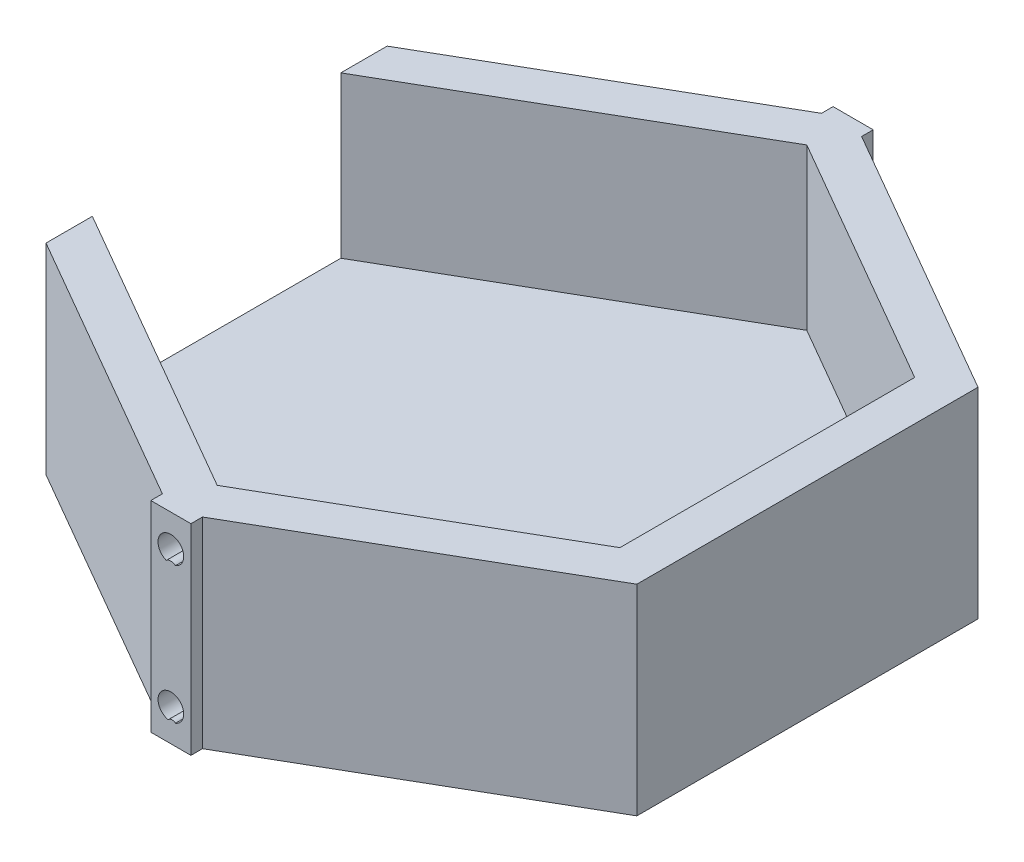
SolidWorks part; units mm, degrees
ref_plane "Front Plane" through (0, 0, 0) normal (0, 0, 1) x (1, 0, 0)
ref_plane "Top Plane" through (0, 0, 0) normal (0, 1, 0) x (1, 0, 0)
ref_plane "Right Plane" through (0, 0, 0) normal (1, 0, 0) x (0, 0, -1)
sketch "Sketch1" plane through (0, 0, 0) normal (0, 1, 0) x (1, 0, 0)
  line L1 (0, 42.5) -> (-36.8061, 21.25)
  line L2 (-36.8061, 21.25) -> (-36.8061, -21.25)
  line L3 (-36.8061, -21.25) -> (0, -42.5)
  line L4 (0, -42.5) -> (36.8061, -21.25)
  line L5 (36.8061, -21.25) -> (36.8061, 21.25)
  line L6 (36.8061, 21.25) -> (0, 42.5)
  circle A0 centre (0, 0) radius 36.8061 construction
  dimension "D1" = 85
extrude "Boss-Extrude1" add sketch "Sketch1" along normal blind 25
shell "Shell1" thickness 5
ref_plane "Plane1" through (-36.8061, 0, -21.25) normal (0, 0, 1) x (1, 0, 0)
ref_plane "Plane2" through (0, 0, -42.5) normal (0, 0, 1) x (1, 0, 0)
sketch "Sketch3" plane through (0, 0, -42.5) normal (0, 0, 1) x (1, 0, 0)
  line L0 (0, 25) -> (0, 0) construction
  line L1 (2.5, 0) -> (-2.5, 0)
  line L2 (2.5, 0) -> (2.5, 25)
  line L3 (2.5, 25) -> (-2.5, 25)
  line L4 (-2.5, 0) -> (-2.5, 25)
  line L5 (2.5, 0) -> (-2.5, 25) construction
  line L6 (2.5, 25) -> (-2.5, 0) construction
  line L7 (0, 25) -> (-36.8061, 25) construction
  point P0 (0, 12.5)
  dimension "D1" = 5
extrude "Boss-Extrude3" add sketch "Sketch3" along normal blind 5
sketch "Sketch4" plane through (0, 0, -42.5) normal (0, 0, -1) x (-1, 0, 0)
  line L0 (0, 4) -> (0, 21) construction
  line L1 (-2.5, 25) -> (-2.5, 0) construction
  circle A0 centre (0, 21) radius 1.6
  circle A1 centre (0, 4) radius 1.6
  arc A2 (-0.5736, 19.5064) -> (0.5736, 19.5064) centre (0, 18.8205) cw
  arc A3 (0.3291, 2.4342) -> (-0.5736, 2.5064) centre (-0.1583, 2.0189) ccw
  point P4 (0, 12.5)
  point P9 (-2.5, 12.5)
  dimension "D2" = 3.2
  dimension "D1" = 17
extrude "Cut-Extrude1" cut sketch "Sketch4" against normal blind 4.5 contours A0 A2 | A3 A1
mirror "Mirror1" about plane through (0, 0, 0) normal (0, 0, 1) of "Cut-Extrude1", "Boss-Extrude3"
